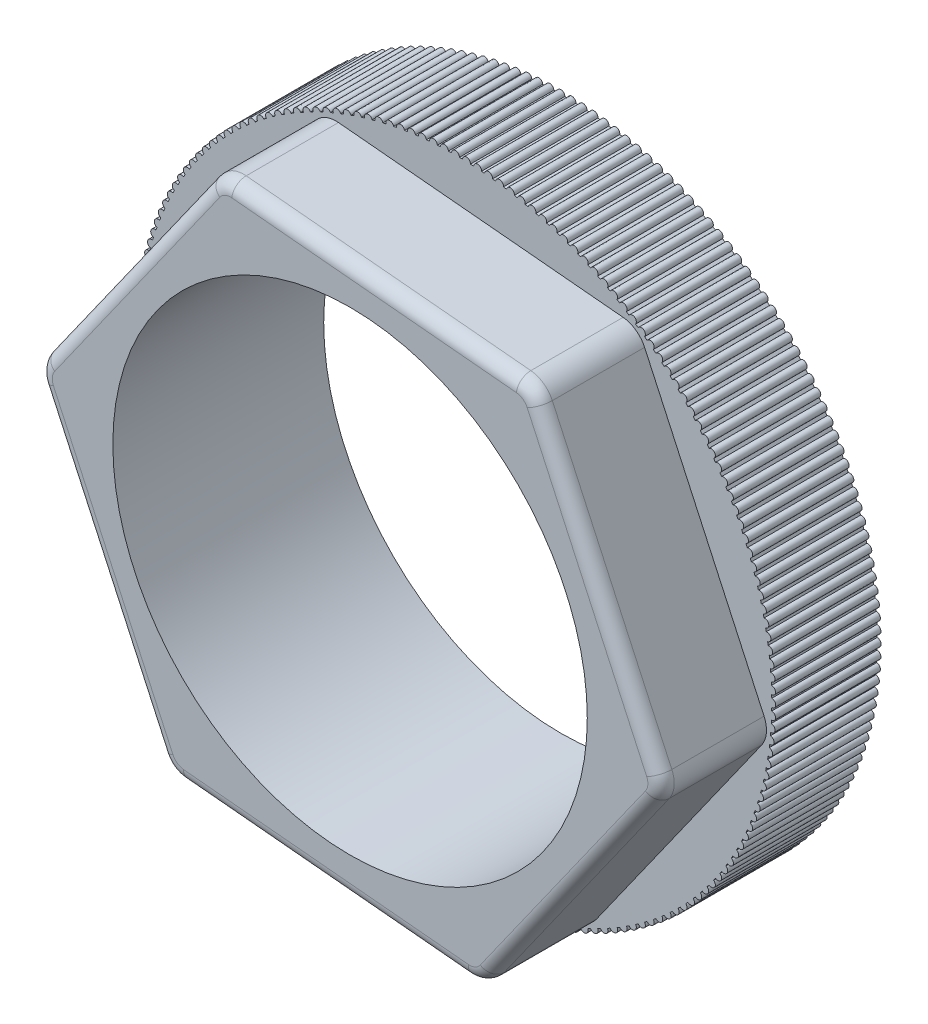
SolidWorks part; units mm, degrees
ref_plane "Alzado" through (0, 0, 0) normal (0, 0, 1) x (1, 0, 0)
ref_plane "Planta" through (0, 0, 0) normal (0, 1, 0) x (1, 0, 0)
ref_plane "Vista lateral" through (0, 0, 0) normal (1, 0, 0) x (0, 0, -1)
sketch "Croquis1" plane through (0, 0, 0) normal (0, 0, 1) x (1, 0, 0)
  circle A0 centre (0, 0) radius 9
  circle A1 centre (0, 0) radius 12
  dimension "D2" = 18
  dimension "D1" = 24
extrude "Saliente-Extruir1" add sketch "Croquis1" along normal blind 4
sketch "Croquis2" plane through (0, 0, 4) normal (0, 0, 1) x (1, 0, 0)
  line L0 (-12, 0) -> (12, 0) construction
  line L1 (0, 12) -> (0, -12) construction
  circle A0 centre (0, 0) radius 12 construction
  arc A1 (0.15, 11.9991) -> (-0.15, 11.9991) centre (0, 12) ccw
  arc A2 (0.15, 11.9991) -> (-0.15, 11.9991) centre (0, 0) ccw
  arc A3 (0.5687, 11.9865) -> (0.2689, 11.997) centre (0, 0) ccw
  arc A4 (0.5687, 11.9865) -> (0.2689, 11.997) centre (0.4188, 11.9927) ccw
  arc A5 (0.9866, 11.9594) -> (0.6874, 11.9803) centre (0, 0) ccw
  arc A6 (0.9866, 11.9594) -> (0.6874, 11.9803) centre (0.8371, 11.9708) ccw
  arc A7 (1.4034, 11.9177) -> (1.1051, 11.949) centre (0, 0) ccw
  arc A8 (1.4034, 11.9177) -> (1.1051, 11.949) centre (1.2543, 11.9343) ccw
  arc A9 (1.8185, 11.8614) -> (1.5214, 11.9032) centre (0, 0) ccw
  arc A10 (1.8185, 11.8614) -> (1.5214, 11.9032) centre (1.6701, 11.8832) ccw
  arc A11 (2.2313, 11.7907) -> (1.9359, 11.8428) centre (0, 0) ccw
  arc A12 (2.2313, 11.7907) -> (1.9359, 11.8428) centre (2.0838, 11.8177) ccw
  arc A13 (2.6415, 11.7057) -> (2.348, 11.768) centre (0, 0) ccw
  arc A14 (2.6415, 11.7057) -> (2.348, 11.768) centre (2.4949, 11.7378) ccw
  arc A15 (3.0484, 11.6064) -> (2.7573, 11.6789) centre (0, 0) ccw
  arc A16 (3.0484, 11.6064) -> (2.7573, 11.6789) centre (2.9031, 11.6435) ccw
  arc A17 (3.4516, 11.4929) -> (3.1632, 11.5756) centre (0, 0) ccw
  arc A18 (3.4516, 11.4929) -> (3.1632, 11.5756) centre (3.3076, 11.5351) ccw
  arc A19 (3.8506, 11.3654) -> (3.5653, 11.4581) centre (0, 0) ccw
  arc A20 (3.8506, 11.3654) -> (3.5653, 11.4581) centre (3.7082, 11.4127) ccw
  arc A21 (4.2449, 11.2241) -> (3.963, 11.3267) centre (0, 0) ccw
  arc A22 (4.2449, 11.2241) -> (3.963, 11.3267) centre (4.1042, 11.2763) ccw
  arc A23 (4.634, 11.0691) -> (4.3559, 11.1815) centre (0, 0) ccw
  arc A24 (4.634, 11.0691) -> (4.3559, 11.1815) centre (4.4953, 11.1262) ccw
  arc A25 (5.0175, 10.9007) -> (4.7434, 11.0227) centre (0, 0) ccw
  arc A26 (5.0175, 10.9007) -> (4.7434, 11.0227) centre (4.8808, 10.9625) ccw
  arc A27 (5.3949, 10.7189) -> (5.1252, 10.8504) centre (0, 0) ccw
  arc A28 (5.3949, 10.7189) -> (5.1252, 10.8504) centre (5.2605, 10.7855) ccw
  arc A29 (5.7657, 10.5241) -> (5.5008, 10.665) centre (0, 0) ccw
  arc A30 (5.7657, 10.5241) -> (5.5008, 10.665) centre (5.6337, 10.5954) ccw
  arc A31 (6.1294, 10.3165) -> (5.8696, 10.4665) centre (0, 0) ccw
  arc A32 (6.1294, 10.3165) -> (5.8696, 10.4665) centre (6, 10.3923) ccw
  arc A33 (6.4857, 10.0963) -> (6.2313, 10.2553) centre (0, 0) ccw
  arc A34 (6.4857, 10.0963) -> (6.2313, 10.2553) centre (6.359, 10.1766) ccw
  arc A35 (6.8341, 9.8638) -> (6.5854, 10.0316) centre (0, 0) ccw
  arc A36 (6.8341, 9.8638) -> (6.5854, 10.0316) centre (6.7103, 9.9485) ccw
  arc A37 (7.1742, 9.6193) -> (6.9315, 9.7956) centre (0, 0) ccw
  arc A38 (7.1742, 9.6193) -> (6.9315, 9.7956) centre (7.0534, 9.7082) ccw
  arc A39 (7.5056, 9.363) -> (7.2692, 9.5477) centre (0, 0) ccw
  arc A40 (7.5056, 9.363) -> (7.2692, 9.5477) centre (7.3879, 9.4561) ccw
  arc A41 (7.8278, 9.0954) -> (7.5979, 9.2882) centre (0, 0) ccw
  arc A42 (7.8278, 9.0954) -> (7.5979, 9.2882) centre (7.7135, 9.1925) ccw
  arc A43 (8.1404, 8.8167) -> (7.9175, 9.0174) centre (0, 0) ccw
  arc A44 (8.1404, 8.8167) -> (7.9175, 9.0174) centre (8.0296, 8.9177) ccw
  arc A45 (8.4431, 8.5272) -> (8.2274, 8.7356) centre (0, 0) ccw
  arc A46 (8.4431, 8.5272) -> (8.2274, 8.7356) centre (8.3359, 8.6321) ccw
  arc A47 (8.7356, 8.2274) -> (8.5272, 8.4431) centre (0, 0) ccw
  arc A48 (8.7356, 8.2274) -> (8.5272, 8.4431) centre (8.6321, 8.3359) ccw
  arc A49 (9.0174, 7.9175) -> (8.8167, 8.1404) centre (0, 0) ccw
  arc A50 (9.0174, 7.9175) -> (8.8167, 8.1404) centre (8.9177, 8.0296) ccw
  arc A51 (9.2882, 7.5979) -> (9.0954, 7.8278) centre (0, 0) ccw
  arc A52 (9.2882, 7.5979) -> (9.0954, 7.8278) centre (9.1925, 7.7135) ccw
  arc A53 (9.5477, 7.2692) -> (9.363, 7.5056) centre (0, 0) ccw
  arc A54 (9.5477, 7.2692) -> (9.363, 7.5056) centre (9.4561, 7.3879) ccw
  arc A55 (9.7956, 6.9315) -> (9.6193, 7.1742) centre (0, 0) ccw
  arc A56 (9.7956, 6.9315) -> (9.6193, 7.1742) centre (9.7082, 7.0534) ccw
  arc A57 (10.0316, 6.5854) -> (9.8638, 6.8341) centre (0, 0) ccw
  arc A58 (10.0316, 6.5854) -> (9.8638, 6.8341) centre (9.9485, 6.7103) ccw
  arc A59 (10.2553, 6.2313) -> (10.0963, 6.4857) centre (0, 0) ccw
  arc A60 (10.2553, 6.2313) -> (10.0963, 6.4857) centre (10.1766, 6.359) ccw
  arc A61 (10.4665, 5.8696) -> (10.3165, 6.1294) centre (0, 0) ccw
  arc A62 (10.4665, 5.8696) -> (10.3165, 6.1294) centre (10.3923, 6) ccw
  arc A63 (10.665, 5.5008) -> (10.5241, 5.7657) centre (0, 0) ccw
  arc A64 (10.665, 5.5008) -> (10.5241, 5.7657) centre (10.5954, 5.6337) ccw
  arc A65 (10.8504, 5.1252) -> (10.7189, 5.3949) centre (0, 0) ccw
  arc A66 (10.8504, 5.1252) -> (10.7189, 5.3949) centre (10.7855, 5.2605) ccw
  arc A67 (11.0227, 4.7434) -> (10.9007, 5.0175) centre (0, 0) ccw
  arc A68 (11.0227, 4.7434) -> (10.9007, 5.0175) centre (10.9625, 4.8808) ccw
  arc A69 (11.1815, 4.3559) -> (11.0691, 4.634) centre (0, 0) ccw
  arc A70 (11.1815, 4.3559) -> (11.0691, 4.634) centre (11.1262, 4.4953) ccw
  arc A71 (11.3267, 3.963) -> (11.2241, 4.2449) centre (0, 0) ccw
  arc A72 (11.3267, 3.963) -> (11.2241, 4.2449) centre (11.2763, 4.1042) ccw
  arc A73 (11.4581, 3.5653) -> (11.3654, 3.8506) centre (0, 0) ccw
  arc A74 (11.4581, 3.5653) -> (11.3654, 3.8506) centre (11.4127, 3.7082) ccw
  arc A75 (11.5756, 3.1632) -> (11.4929, 3.4516) centre (0, 0) ccw
  arc A76 (11.5756, 3.1632) -> (11.4929, 3.4516) centre (11.5351, 3.3076) ccw
  arc A77 (11.6789, 2.7573) -> (11.6064, 3.0484) centre (0, 0) ccw
  arc A78 (11.6789, 2.7573) -> (11.6064, 3.0484) centre (11.6435, 2.9031) ccw
  arc A79 (11.768, 2.348) -> (11.7057, 2.6415) centre (0, 0) ccw
  arc A80 (11.768, 2.348) -> (11.7057, 2.6415) centre (11.7378, 2.4949) ccw
  arc A81 (11.8428, 1.9359) -> (11.7907, 2.2313) centre (0, 0) ccw
  arc A82 (11.8428, 1.9359) -> (11.7907, 2.2313) centre (11.8177, 2.0838) ccw
  arc A83 (11.9032, 1.5214) -> (11.8614, 1.8185) centre (0, 0) ccw
  arc A84 (11.9032, 1.5214) -> (11.8614, 1.8185) centre (11.8832, 1.6701) ccw
  arc A85 (11.949, 1.1051) -> (11.9177, 1.4034) centre (0, 0) ccw
  arc A86 (11.949, 1.1051) -> (11.9177, 1.4034) centre (11.9343, 1.2543) ccw
  arc A87 (11.9803, 0.6874) -> (11.9594, 0.9866) centre (0, 0) ccw
  arc A88 (11.9803, 0.6874) -> (11.9594, 0.9866) centre (11.9708, 0.8371) ccw
  arc A89 (11.997, 0.2689) -> (11.9865, 0.5687) centre (0, 0) ccw
  arc A90 (11.997, 0.2689) -> (11.9865, 0.5687) centre (11.9927, 0.4188) ccw
  arc A91 (11.9991, -0.15) -> (11.9991, 0.15) centre (0, 0) ccw
  arc A92 (11.9991, -0.15) -> (11.9991, 0.15) centre (12, 0) ccw
  arc A93 (11.9865, -0.5687) -> (11.997, -0.2689) centre (0, 0) ccw
  arc A94 (11.9865, -0.5687) -> (11.997, -0.2689) centre (11.9927, -0.4188) ccw
  arc A95 (11.9594, -0.9866) -> (11.9803, -0.6874) centre (0, 0) ccw
  arc A96 (11.9594, -0.9866) -> (11.9803, -0.6874) centre (11.9708, -0.8371) ccw
  arc A97 (11.9177, -1.4034) -> (11.949, -1.1051) centre (0, 0) ccw
  arc A98 (11.9177, -1.4034) -> (11.949, -1.1051) centre (11.9343, -1.2543) ccw
  arc A99 (11.8614, -1.8185) -> (11.9032, -1.5214) centre (0, 0) ccw
  arc A100 (11.8614, -1.8185) -> (11.9032, -1.5214) centre (11.8832, -1.6701) ccw
  arc A101 (11.7907, -2.2313) -> (11.8428, -1.9359) centre (0, 0) ccw
  arc A102 (11.7907, -2.2313) -> (11.8428, -1.9359) centre (11.8177, -2.0838) ccw
  arc A103 (11.7057, -2.6415) -> (11.768, -2.348) centre (0, 0) ccw
  arc A104 (11.7057, -2.6415) -> (11.768, -2.348) centre (11.7378, -2.4949) ccw
  arc A105 (11.6064, -3.0484) -> (11.6789, -2.7573) centre (0, 0) ccw
  arc A106 (11.6064, -3.0484) -> (11.6789, -2.7573) centre (11.6435, -2.9031) ccw
  arc A107 (11.4929, -3.4516) -> (11.5756, -3.1632) centre (0, 0) ccw
  arc A108 (11.4929, -3.4516) -> (11.5756, -3.1632) centre (11.5351, -3.3076) ccw
  arc A109 (11.3654, -3.8506) -> (11.4581, -3.5653) centre (0, 0) ccw
  arc A110 (11.3654, -3.8506) -> (11.4581, -3.5653) centre (11.4127, -3.7082) ccw
  arc A111 (11.2241, -4.2449) -> (11.3267, -3.963) centre (0, 0) ccw
  arc A112 (11.2241, -4.2449) -> (11.3267, -3.963) centre (11.2763, -4.1042) ccw
  arc A113 (11.0691, -4.634) -> (11.1815, -4.3559) centre (0, 0) ccw
  arc A114 (11.0691, -4.634) -> (11.1815, -4.3559) centre (11.1262, -4.4953) ccw
  arc A115 (10.9007, -5.0175) -> (11.0227, -4.7434) centre (0, 0) ccw
  arc A116 (10.9007, -5.0175) -> (11.0227, -4.7434) centre (10.9625, -4.8808) ccw
  arc A117 (10.7189, -5.3949) -> (10.8504, -5.1252) centre (0, 0) ccw
  arc A118 (10.7189, -5.3949) -> (10.8504, -5.1252) centre (10.7855, -5.2605) ccw
  arc A119 (10.5241, -5.7657) -> (10.665, -5.5008) centre (0, 0) ccw
  arc A120 (10.5241, -5.7657) -> (10.665, -5.5008) centre (10.5954, -5.6337) ccw
  arc A121 (10.3165, -6.1294) -> (10.4665, -5.8696) centre (0, 0) ccw
  arc A122 (10.3165, -6.1294) -> (10.4665, -5.8696) centre (10.3923, -6) ccw
  arc A123 (10.0963, -6.4857) -> (10.2553, -6.2313) centre (0, 0) ccw
  arc A124 (10.0963, -6.4857) -> (10.2553, -6.2313) centre (10.1766, -6.359) ccw
  arc A125 (9.8638, -6.8341) -> (10.0316, -6.5854) centre (0, 0) ccw
  arc A126 (9.8638, -6.8341) -> (10.0316, -6.5854) centre (9.9485, -6.7103) ccw
  arc A127 (9.6193, -7.1742) -> (9.7956, -6.9315) centre (0, 0) ccw
  arc A128 (9.6193, -7.1742) -> (9.7956, -6.9315) centre (9.7082, -7.0534) ccw
  arc A129 (9.363, -7.5056) -> (9.5477, -7.2692) centre (0, 0) ccw
  arc A130 (9.363, -7.5056) -> (9.5477, -7.2692) centre (9.4561, -7.3879) ccw
  arc A131 (9.0954, -7.8278) -> (9.2882, -7.5979) centre (0, 0) ccw
  arc A132 (9.0954, -7.8278) -> (9.2882, -7.5979) centre (9.1925, -7.7135) ccw
  arc A133 (8.8167, -8.1404) -> (9.0174, -7.9175) centre (0, 0) ccw
  arc A134 (8.8167, -8.1404) -> (9.0174, -7.9175) centre (8.9177, -8.0296) ccw
  arc A135 (8.5272, -8.4431) -> (8.7356, -8.2274) centre (0, 0) ccw
  arc A136 (8.5272, -8.4431) -> (8.7356, -8.2274) centre (8.6321, -8.3359) ccw
  arc A137 (8.2274, -8.7356) -> (8.4431, -8.5272) centre (0, 0) ccw
  arc A138 (8.2274, -8.7356) -> (8.4431, -8.5272) centre (8.3359, -8.6321) ccw
  arc A139 (7.9175, -9.0174) -> (8.1404, -8.8167) centre (0, 0) ccw
  arc A140 (7.9175, -9.0174) -> (8.1404, -8.8167) centre (8.0296, -8.9177) ccw
  arc A141 (7.5979, -9.2882) -> (7.8278, -9.0954) centre (0, 0) ccw
  arc A142 (7.5979, -9.2882) -> (7.8278, -9.0954) centre (7.7135, -9.1925) ccw
  arc A143 (7.2692, -9.5477) -> (7.5056, -9.363) centre (0, 0) ccw
  arc A144 (7.2692, -9.5477) -> (7.5056, -9.363) centre (7.3879, -9.4561) ccw
  arc A145 (6.9315, -9.7956) -> (7.1742, -9.6193) centre (0, 0) ccw
  arc A146 (6.9315, -9.7956) -> (7.1742, -9.6193) centre (7.0534, -9.7082) ccw
  arc A147 (6.5854, -10.0316) -> (6.8341, -9.8638) centre (0, 0) ccw
  arc A148 (6.5854, -10.0316) -> (6.8341, -9.8638) centre (6.7103, -9.9485) ccw
  arc A149 (6.2313, -10.2553) -> (6.4857, -10.0963) centre (0, 0) ccw
  arc A150 (6.2313, -10.2553) -> (6.4857, -10.0963) centre (6.359, -10.1766) ccw
  arc A151 (5.8696, -10.4665) -> (6.1294, -10.3165) centre (0, 0) ccw
  arc A152 (5.8696, -10.4665) -> (6.1294, -10.3165) centre (6, -10.3923) ccw
  arc A153 (5.5008, -10.665) -> (5.7657, -10.5241) centre (0, 0) ccw
  arc A154 (5.5008, -10.665) -> (5.7657, -10.5241) centre (5.6337, -10.5954) ccw
  arc A155 (5.1252, -10.8504) -> (5.3949, -10.7189) centre (0, 0) ccw
  arc A156 (5.1252, -10.8504) -> (5.3949, -10.7189) centre (5.2605, -10.7855) ccw
  arc A157 (4.7434, -11.0227) -> (5.0175, -10.9007) centre (0, 0) ccw
  arc A158 (4.7434, -11.0227) -> (5.0175, -10.9007) centre (4.8808, -10.9625) ccw
  arc A159 (4.3559, -11.1815) -> (4.634, -11.0691) centre (0, 0) ccw
  arc A160 (4.3559, -11.1815) -> (4.634, -11.0691) centre (4.4953, -11.1262) ccw
  arc A161 (3.963, -11.3267) -> (4.2449, -11.2241) centre (0, 0) ccw
  arc A162 (3.963, -11.3267) -> (4.2449, -11.2241) centre (4.1042, -11.2763) ccw
  arc A163 (3.5653, -11.4581) -> (3.8506, -11.3654) centre (0, 0) ccw
  arc A164 (3.5653, -11.4581) -> (3.8506, -11.3654) centre (3.7082, -11.4127) ccw
  arc A165 (3.1632, -11.5756) -> (3.4516, -11.4929) centre (0, 0) ccw
  arc A166 (3.1632, -11.5756) -> (3.4516, -11.4929) centre (3.3076, -11.5351) ccw
  arc A167 (2.7573, -11.6789) -> (3.0484, -11.6064) centre (0, 0) ccw
  arc A168 (2.7573, -11.6789) -> (3.0484, -11.6064) centre (2.9031, -11.6435) ccw
  arc A169 (2.348, -11.768) -> (2.6415, -11.7057) centre (0, 0) ccw
  arc A170 (2.348, -11.768) -> (2.6415, -11.7057) centre (2.4949, -11.7378) ccw
  arc A171 (1.9359, -11.8428) -> (2.2313, -11.7907) centre (0, 0) ccw
  arc A172 (1.9359, -11.8428) -> (2.2313, -11.7907) centre (2.0838, -11.8177) ccw
  arc A173 (1.5214, -11.9032) -> (1.8185, -11.8614) centre (0, 0) ccw
  arc A174 (1.5214, -11.9032) -> (1.8185, -11.8614) centre (1.6701, -11.8832) ccw
  arc A175 (1.1051, -11.949) -> (1.4034, -11.9177) centre (0, 0) ccw
  arc A176 (1.1051, -11.949) -> (1.4034, -11.9177) centre (1.2543, -11.9343) ccw
  arc A177 (0.6874, -11.9803) -> (0.9866, -11.9594) centre (0, 0) ccw
  arc A178 (0.6874, -11.9803) -> (0.9866, -11.9594) centre (0.8371, -11.9708) ccw
  arc A179 (0.2689, -11.997) -> (0.5687, -11.9865) centre (0, 0) ccw
  arc A180 (0.2689, -11.997) -> (0.5687, -11.9865) centre (0.4188, -11.9927) ccw
  arc A181 (-0.15, -11.9991) -> (0.15, -11.9991) centre (0, 0) ccw
  arc A182 (-0.15, -11.9991) -> (0.15, -11.9991) centre (0, -12) ccw
  arc A183 (-0.5687, -11.9865) -> (-0.2689, -11.997) centre (0, 0) ccw
  arc A184 (-0.5687, -11.9865) -> (-0.2689, -11.997) centre (-0.4188, -11.9927) ccw
  arc A185 (-0.9866, -11.9594) -> (-0.6874, -11.9803) centre (0, 0) ccw
  arc A186 (-0.9866, -11.9594) -> (-0.6874, -11.9803) centre (-0.8371, -11.9708) ccw
  arc A187 (-1.4034, -11.9177) -> (-1.1051, -11.949) centre (0, 0) ccw
  arc A188 (-1.4034, -11.9177) -> (-1.1051, -11.949) centre (-1.2543, -11.9343) ccw
  arc A189 (-1.8185, -11.8614) -> (-1.5214, -11.9032) centre (0, 0) ccw
  arc A190 (-1.8185, -11.8614) -> (-1.5214, -11.9032) centre (-1.6701, -11.8832) ccw
  arc A191 (-2.2313, -11.7907) -> (-1.9359, -11.8428) centre (0, 0) ccw
  arc A192 (-2.2313, -11.7907) -> (-1.9359, -11.8428) centre (-2.0838, -11.8177) ccw
  arc A193 (-2.6415, -11.7057) -> (-2.348, -11.768) centre (0, 0) ccw
  arc A194 (-2.6415, -11.7057) -> (-2.348, -11.768) centre (-2.4949, -11.7378) ccw
  arc A195 (-3.0484, -11.6064) -> (-2.7573, -11.6789) centre (0, 0) ccw
  arc A196 (-3.0484, -11.6064) -> (-2.7573, -11.6789) centre (-2.9031, -11.6435) ccw
  arc A197 (-3.4516, -11.4929) -> (-3.1632, -11.5756) centre (0, 0) ccw
  arc A198 (-3.4516, -11.4929) -> (-3.1632, -11.5756) centre (-3.3076, -11.5351) ccw
  arc A199 (-3.8506, -11.3654) -> (-3.5653, -11.4581) centre (0, 0) ccw
  arc A200 (-3.8506, -11.3654) -> (-3.5653, -11.4581) centre (-3.7082, -11.4127) ccw
  arc A201 (-4.2449, -11.2241) -> (-3.963, -11.3267) centre (0, 0) ccw
  arc A202 (-4.2449, -11.2241) -> (-3.963, -11.3267) centre (-4.1042, -11.2763) ccw
  arc A203 (-4.634, -11.0691) -> (-4.3559, -11.1815) centre (0, 0) ccw
  arc A204 (-4.634, -11.0691) -> (-4.3559, -11.1815) centre (-4.4953, -11.1262) ccw
  arc A205 (-5.0175, -10.9007) -> (-4.7434, -11.0227) centre (0, 0) ccw
  arc A206 (-5.0175, -10.9007) -> (-4.7434, -11.0227) centre (-4.8808, -10.9625) ccw
  arc A207 (-5.3949, -10.7189) -> (-5.1252, -10.8504) centre (0, 0) ccw
  arc A208 (-5.3949, -10.7189) -> (-5.1252, -10.8504) centre (-5.2605, -10.7855) ccw
  arc A209 (-5.7657, -10.5241) -> (-5.5008, -10.665) centre (0, 0) ccw
  arc A210 (-5.7657, -10.5241) -> (-5.5008, -10.665) centre (-5.6337, -10.5954) ccw
  arc A211 (-6.1294, -10.3165) -> (-5.8696, -10.4665) centre (0, 0) ccw
  arc A212 (-6.1294, -10.3165) -> (-5.8696, -10.4665) centre (-6, -10.3923) ccw
  arc A213 (-6.4857, -10.0963) -> (-6.2313, -10.2553) centre (0, 0) ccw
  arc A214 (-6.4857, -10.0963) -> (-6.2313, -10.2553) centre (-6.359, -10.1766) ccw
  arc A215 (-6.8341, -9.8638) -> (-6.5854, -10.0316) centre (0, 0) ccw
  arc A216 (-6.8341, -9.8638) -> (-6.5854, -10.0316) centre (-6.7103, -9.9485) ccw
  arc A217 (-7.1742, -9.6193) -> (-6.9315, -9.7956) centre (0, 0) ccw
  arc A218 (-7.1742, -9.6193) -> (-6.9315, -9.7956) centre (-7.0534, -9.7082) ccw
  arc A219 (-7.5056, -9.363) -> (-7.2692, -9.5477) centre (0, 0) ccw
  arc A220 (-7.5056, -9.363) -> (-7.2692, -9.5477) centre (-7.3879, -9.4561) ccw
  arc A221 (-7.8278, -9.0954) -> (-7.5979, -9.2882) centre (0, 0) ccw
  arc A222 (-7.8278, -9.0954) -> (-7.5979, -9.2882) centre (-7.7135, -9.1925) ccw
  arc A223 (-8.1404, -8.8167) -> (-7.9175, -9.0174) centre (0, 0) ccw
  arc A224 (-8.1404, -8.8167) -> (-7.9175, -9.0174) centre (-8.0296, -8.9177) ccw
  arc A225 (-8.4431, -8.5272) -> (-8.2274, -8.7356) centre (0, 0) ccw
  arc A226 (-8.4431, -8.5272) -> (-8.2274, -8.7356) centre (-8.3359, -8.6321) ccw
  arc A227 (-8.7356, -8.2274) -> (-8.5272, -8.4431) centre (0, 0) ccw
  arc A228 (-8.7356, -8.2274) -> (-8.5272, -8.4431) centre (-8.6321, -8.3359) ccw
  arc A229 (-9.0174, -7.9175) -> (-8.8167, -8.1404) centre (0, 0) ccw
  arc A230 (-9.0174, -7.9175) -> (-8.8167, -8.1404) centre (-8.9177, -8.0296) ccw
  arc A231 (-9.2882, -7.5979) -> (-9.0954, -7.8278) centre (0, 0) ccw
  arc A232 (-9.2882, -7.5979) -> (-9.0954, -7.8278) centre (-9.1925, -7.7135) ccw
  arc A233 (-9.5477, -7.2692) -> (-9.363, -7.5056) centre (0, 0) ccw
  arc A234 (-9.5477, -7.2692) -> (-9.363, -7.5056) centre (-9.4561, -7.3879) ccw
  arc A235 (-9.7956, -6.9315) -> (-9.6193, -7.1742) centre (0, 0) ccw
  arc A236 (-9.7956, -6.9315) -> (-9.6193, -7.1742) centre (-9.7082, -7.0534) ccw
  arc A237 (-10.0316, -6.5854) -> (-9.8638, -6.8341) centre (0, 0) ccw
  arc A238 (-10.0316, -6.5854) -> (-9.8638, -6.8341) centre (-9.9485, -6.7103) ccw
  arc A239 (-10.2553, -6.2313) -> (-10.0963, -6.4857) centre (0, 0) ccw
  arc A240 (-10.2553, -6.2313) -> (-10.0963, -6.4857) centre (-10.1766, -6.359) ccw
  arc A241 (-10.4665, -5.8696) -> (-10.3165, -6.1294) centre (0, 0) ccw
  arc A242 (-10.4665, -5.8696) -> (-10.3165, -6.1294) centre (-10.3923, -6) ccw
  arc A243 (-10.665, -5.5008) -> (-10.5241, -5.7657) centre (0, 0) ccw
  arc A244 (-10.665, -5.5008) -> (-10.5241, -5.7657) centre (-10.5954, -5.6337) ccw
  arc A245 (-10.8504, -5.1252) -> (-10.7189, -5.3949) centre (0, 0) ccw
  arc A246 (-10.8504, -5.1252) -> (-10.7189, -5.3949) centre (-10.7855, -5.2605) ccw
  arc A247 (-11.0227, -4.7434) -> (-10.9007, -5.0175) centre (0, 0) ccw
  arc A248 (-11.0227, -4.7434) -> (-10.9007, -5.0175) centre (-10.9625, -4.8808) ccw
  arc A249 (-11.1815, -4.3559) -> (-11.0691, -4.634) centre (0, 0) ccw
  arc A250 (-11.1815, -4.3559) -> (-11.0691, -4.634) centre (-11.1262, -4.4953) ccw
  arc A251 (-11.3267, -3.963) -> (-11.2241, -4.2449) centre (0, 0) ccw
  arc A252 (-11.3267, -3.963) -> (-11.2241, -4.2449) centre (-11.2763, -4.1042) ccw
  arc A253 (-11.4581, -3.5653) -> (-11.3654, -3.8506) centre (0, 0) ccw
  arc A254 (-11.4581, -3.5653) -> (-11.3654, -3.8506) centre (-11.4127, -3.7082) ccw
  arc A255 (-11.5756, -3.1632) -> (-11.4929, -3.4516) centre (0, 0) ccw
  arc A256 (-11.5756, -3.1632) -> (-11.4929, -3.4516) centre (-11.5351, -3.3076) ccw
  arc A257 (-11.6789, -2.7573) -> (-11.6064, -3.0484) centre (0, 0) ccw
  arc A258 (-11.6789, -2.7573) -> (-11.6064, -3.0484) centre (-11.6435, -2.9031) ccw
  arc A259 (-11.768, -2.348) -> (-11.7057, -2.6415) centre (0, 0) ccw
  arc A260 (-11.768, -2.348) -> (-11.7057, -2.6415) centre (-11.7378, -2.4949) ccw
  arc A261 (-11.8428, -1.9359) -> (-11.7907, -2.2313) centre (0, 0) ccw
  arc A262 (-11.8428, -1.9359) -> (-11.7907, -2.2313) centre (-11.8177, -2.0838) ccw
  arc A263 (-11.9032, -1.5214) -> (-11.8614, -1.8185) centre (0, 0) ccw
  arc A264 (-11.9032, -1.5214) -> (-11.8614, -1.8185) centre (-11.8832, -1.6701) ccw
  arc A265 (-11.949, -1.1051) -> (-11.9177, -1.4034) centre (0, 0) ccw
  arc A266 (-11.949, -1.1051) -> (-11.9177, -1.4034) centre (-11.9343, -1.2543) ccw
  arc A267 (-11.9803, -0.6874) -> (-11.9594, -0.9866) centre (0, 0) ccw
  arc A268 (-11.9803, -0.6874) -> (-11.9594, -0.9866) centre (-11.9708, -0.8371) ccw
  arc A269 (-11.997, -0.2689) -> (-11.9865, -0.5687) centre (0, 0) ccw
  arc A270 (-11.997, -0.2689) -> (-11.9865, -0.5687) centre (-11.9927, -0.4188) ccw
  arc A271 (-11.9991, 0.15) -> (-11.9991, -0.15) centre (0, 0) ccw
  arc A272 (-11.9991, 0.15) -> (-11.9991, -0.15) centre (-12, 0) ccw
  arc A273 (-11.9865, 0.5687) -> (-11.997, 0.2689) centre (0, 0) ccw
  arc A274 (-11.9865, 0.5687) -> (-11.997, 0.2689) centre (-11.9927, 0.4188) ccw
  arc A275 (-11.9594, 0.9866) -> (-11.9803, 0.6874) centre (0, 0) ccw
  arc A276 (-11.9594, 0.9866) -> (-11.9803, 0.6874) centre (-11.9708, 0.8371) ccw
  arc A277 (-11.9177, 1.4034) -> (-11.949, 1.1051) centre (0, 0) ccw
  arc A278 (-11.9177, 1.4034) -> (-11.949, 1.1051) centre (-11.9343, 1.2543) ccw
  arc A279 (-11.8614, 1.8185) -> (-11.9032, 1.5214) centre (0, 0) ccw
  arc A280 (-11.8614, 1.8185) -> (-11.9032, 1.5214) centre (-11.8832, 1.6701) ccw
  arc A281 (-11.7907, 2.2313) -> (-11.8428, 1.9359) centre (0, 0) ccw
  arc A282 (-11.7907, 2.2313) -> (-11.8428, 1.9359) centre (-11.8177, 2.0838) ccw
  arc A283 (-11.7057, 2.6415) -> (-11.768, 2.348) centre (0, 0) ccw
  arc A284 (-11.7057, 2.6415) -> (-11.768, 2.348) centre (-11.7378, 2.4949) ccw
  arc A285 (-11.6064, 3.0484) -> (-11.6789, 2.7573) centre (0, 0) ccw
  arc A286 (-11.6064, 3.0484) -> (-11.6789, 2.7573) centre (-11.6435, 2.9031) ccw
  arc A287 (-11.4929, 3.4516) -> (-11.5756, 3.1632) centre (0, 0) ccw
  arc A288 (-11.4929, 3.4516) -> (-11.5756, 3.1632) centre (-11.5351, 3.3076) ccw
  arc A289 (-11.3654, 3.8506) -> (-11.4581, 3.5653) centre (0, 0) ccw
  arc A290 (-11.3654, 3.8506) -> (-11.4581, 3.5653) centre (-11.4127, 3.7082) ccw
  arc A291 (-11.2241, 4.2449) -> (-11.3267, 3.963) centre (0, 0) ccw
  arc A292 (-11.2241, 4.2449) -> (-11.3267, 3.963) centre (-11.2763, 4.1042) ccw
  arc A293 (-11.0691, 4.634) -> (-11.1815, 4.3559) centre (0, 0) ccw
  arc A294 (-11.0691, 4.634) -> (-11.1815, 4.3559) centre (-11.1262, 4.4953) ccw
  arc A295 (-10.9007, 5.0175) -> (-11.0227, 4.7434) centre (0, 0) ccw
  arc A296 (-10.9007, 5.0175) -> (-11.0227, 4.7434) centre (-10.9625, 4.8808) ccw
  arc A297 (-10.7189, 5.3949) -> (-10.8504, 5.1252) centre (0, 0) ccw
  arc A298 (-10.7189, 5.3949) -> (-10.8504, 5.1252) centre (-10.7855, 5.2605) ccw
  arc A299 (-10.5241, 5.7657) -> (-10.665, 5.5008) centre (0, 0) ccw
  arc A300 (-10.5241, 5.7657) -> (-10.665, 5.5008) centre (-10.5954, 5.6337) ccw
  arc A301 (-10.3165, 6.1294) -> (-10.4665, 5.8696) centre (0, 0) ccw
  arc A302 (-10.3165, 6.1294) -> (-10.4665, 5.8696) centre (-10.3923, 6) ccw
  arc A303 (-10.0963, 6.4857) -> (-10.2553, 6.2313) centre (0, 0) ccw
  arc A304 (-10.0963, 6.4857) -> (-10.2553, 6.2313) centre (-10.1766, 6.359) ccw
  arc A305 (-9.8638, 6.8341) -> (-10.0316, 6.5854) centre (0, 0) ccw
  arc A306 (-9.8638, 6.8341) -> (-10.0316, 6.5854) centre (-9.9485, 6.7103) ccw
  arc A307 (-9.6193, 7.1742) -> (-9.7956, 6.9315) centre (0, 0) ccw
  arc A308 (-9.6193, 7.1742) -> (-9.7956, 6.9315) centre (-9.7082, 7.0534) ccw
  arc A309 (-9.363, 7.5056) -> (-9.5477, 7.2692) centre (0, 0) ccw
  arc A310 (-9.363, 7.5056) -> (-9.5477, 7.2692) centre (-9.4561, 7.3879) ccw
  arc A311 (-9.0954, 7.8278) -> (-9.2882, 7.5979) centre (0, 0) ccw
  arc A312 (-9.0954, 7.8278) -> (-9.2882, 7.5979) centre (-9.1925, 7.7135) ccw
  arc A313 (-8.8167, 8.1404) -> (-9.0174, 7.9175) centre (0, 0) ccw
  arc A314 (-8.8167, 8.1404) -> (-9.0174, 7.9175) centre (-8.9177, 8.0296) ccw
  arc A315 (-8.5272, 8.4431) -> (-8.7356, 8.2274) centre (0, 0) ccw
  arc A316 (-8.5272, 8.4431) -> (-8.7356, 8.2274) centre (-8.6321, 8.3359) ccw
  arc A317 (-8.2274, 8.7356) -> (-8.4431, 8.5272) centre (0, 0) ccw
  arc A318 (-8.2274, 8.7356) -> (-8.4431, 8.5272) centre (-8.3359, 8.6321) ccw
  arc A319 (-7.9175, 9.0174) -> (-8.1404, 8.8167) centre (0, 0) ccw
  arc A320 (-7.9175, 9.0174) -> (-8.1404, 8.8167) centre (-8.0296, 8.9177) ccw
  arc A321 (-7.5979, 9.2882) -> (-7.8278, 9.0954) centre (0, 0) ccw
  arc A322 (-7.5979, 9.2882) -> (-7.8278, 9.0954) centre (-7.7135, 9.1925) ccw
  arc A323 (-7.2692, 9.5477) -> (-7.5056, 9.363) centre (0, 0) ccw
  arc A324 (-7.2692, 9.5477) -> (-7.5056, 9.363) centre (-7.3879, 9.4561) ccw
  arc A325 (-6.9315, 9.7956) -> (-7.1742, 9.6193) centre (0, 0) ccw
  arc A326 (-6.9315, 9.7956) -> (-7.1742, 9.6193) centre (-7.0534, 9.7082) ccw
  arc A327 (-6.5854, 10.0316) -> (-6.8341, 9.8638) centre (0, 0) ccw
  arc A328 (-6.5854, 10.0316) -> (-6.8341, 9.8638) centre (-6.7103, 9.9485) ccw
  arc A329 (-6.2313, 10.2553) -> (-6.4857, 10.0963) centre (0, 0) ccw
  arc A330 (-6.2313, 10.2553) -> (-6.4857, 10.0963) centre (-6.359, 10.1766) ccw
  arc A331 (-5.8696, 10.4665) -> (-6.1294, 10.3165) centre (0, 0) ccw
  arc A332 (-5.8696, 10.4665) -> (-6.1294, 10.3165) centre (-6, 10.3923) ccw
  arc A333 (-5.5008, 10.665) -> (-5.7657, 10.5241) centre (0, 0) ccw
  arc A334 (-5.5008, 10.665) -> (-5.7657, 10.5241) centre (-5.6337, 10.5954) ccw
  arc A335 (-5.1252, 10.8504) -> (-5.3949, 10.7189) centre (0, 0) ccw
  arc A336 (-5.1252, 10.8504) -> (-5.3949, 10.7189) centre (-5.2605, 10.7855) ccw
  arc A337 (-4.7434, 11.0227) -> (-5.0175, 10.9007) centre (0, 0) ccw
  arc A338 (-4.7434, 11.0227) -> (-5.0175, 10.9007) centre (-4.8808, 10.9625) ccw
  arc A339 (-4.3559, 11.1815) -> (-4.634, 11.0691) centre (0, 0) ccw
  arc A340 (-4.3559, 11.1815) -> (-4.634, 11.0691) centre (-4.4953, 11.1262) ccw
  arc A341 (-3.963, 11.3267) -> (-4.2449, 11.2241) centre (0, 0) ccw
  arc A342 (-3.963, 11.3267) -> (-4.2449, 11.2241) centre (-4.1042, 11.2763) ccw
  arc A343 (-3.5653, 11.4581) -> (-3.8506, 11.3654) centre (0, 0) ccw
  arc A344 (-3.5653, 11.4581) -> (-3.8506, 11.3654) centre (-3.7082, 11.4127) ccw
  arc A345 (-3.1632, 11.5756) -> (-3.4516, 11.4929) centre (0, 0) ccw
  arc A346 (-3.1632, 11.5756) -> (-3.4516, 11.4929) centre (-3.3076, 11.5351) ccw
  arc A347 (-2.7573, 11.6789) -> (-3.0484, 11.6064) centre (0, 0) ccw
  arc A348 (-2.7573, 11.6789) -> (-3.0484, 11.6064) centre (-2.9031, 11.6435) ccw
  arc A349 (-2.348, 11.768) -> (-2.6415, 11.7057) centre (0, 0) ccw
  arc A350 (-2.348, 11.768) -> (-2.6415, 11.7057) centre (-2.4949, 11.7378) ccw
  arc A351 (-1.9359, 11.8428) -> (-2.2313, 11.7907) centre (0, 0) ccw
  arc A352 (-1.9359, 11.8428) -> (-2.2313, 11.7907) centre (-2.0838, 11.8177) ccw
  arc A353 (-1.5214, 11.9032) -> (-1.8185, 11.8614) centre (0, 0) ccw
  arc A354 (-1.5214, 11.9032) -> (-1.8185, 11.8614) centre (-1.6701, 11.8832) ccw
  arc A355 (-1.1051, 11.949) -> (-1.4034, 11.9177) centre (0, 0) ccw
  arc A356 (-1.1051, 11.949) -> (-1.4034, 11.9177) centre (-1.2543, 11.9343) ccw
  arc A357 (-0.6874, 11.9803) -> (-0.9866, 11.9594) centre (0, 0) ccw
  arc A358 (-0.6874, 11.9803) -> (-0.9866, 11.9594) centre (-0.8371, 11.9708) ccw
  arc A359 (-0.2689, 11.997) -> (-0.5687, 11.9865) centre (0, 0) ccw
  arc A360 (-0.2689, 11.997) -> (-0.5687, 11.9865) centre (-0.4188, 11.9927) ccw
  point P550 (0, 0)
  dimension "D1" = 0.3
  dimension "D2" = 180
extrude "Saliente-Extruir4" add sketch "Croquis2" against normal blind 4
sketch "Croquis3" plane through (0, 0, 4) normal (0, 0, 1) x (1, 0, 0)
  line L1 (-5.0153, 10.9017) -> (-11.9488, 1.1075)
  line L2 (-11.9488, 1.1075) -> (-6.9335, -9.7942)
  line L3 (-6.9335, -9.7942) -> (5.0153, -10.9017)
  line L4 (5.0153, -10.9017) -> (11.9488, -1.1075)
  line L5 (11.9488, -1.1075) -> (6.9335, 9.7942)
  line L6 (6.9335, 9.7942) -> (-5.0153, 10.9017)
  circle A0 centre (0, 0) radius 12 construction
  circle A1 centre (0, 0) radius 9
  dimension "D1" = 24
  dimension "D2" = 18
extrude "Saliente-Extruir5" add sketch "Croquis3" along normal blind 4
fillet "Redondeo1" radius 1 6 edges at (5.0153, -10.9017, 6) (-6.9335, -9.7942, 6) (-11.9488, 1.1075, 6) (-5.0153, 10.9017, 6) (6.9335, 9.7942, 6) (11.9488, -1.1075, 6)
fillet "Redondeo2" radius 0.5 12 edges at (11.7947, -1.0932, 8) (8.482, -6.0046, 8) (4.9506, -10.7611, 8) (-0.9591, -10.348, 8) (-6.8441, -9.668, 8) (-9.4411, -4.3434, 8) (-11.7947, 1.0932, 8) (-8.482, 6.0046, 8) (-4.9506, 10.7611, 8) (0.9591, 10.348, 8) (6.8441, 9.668, 8) (9.4411, 4.3434, 8)
